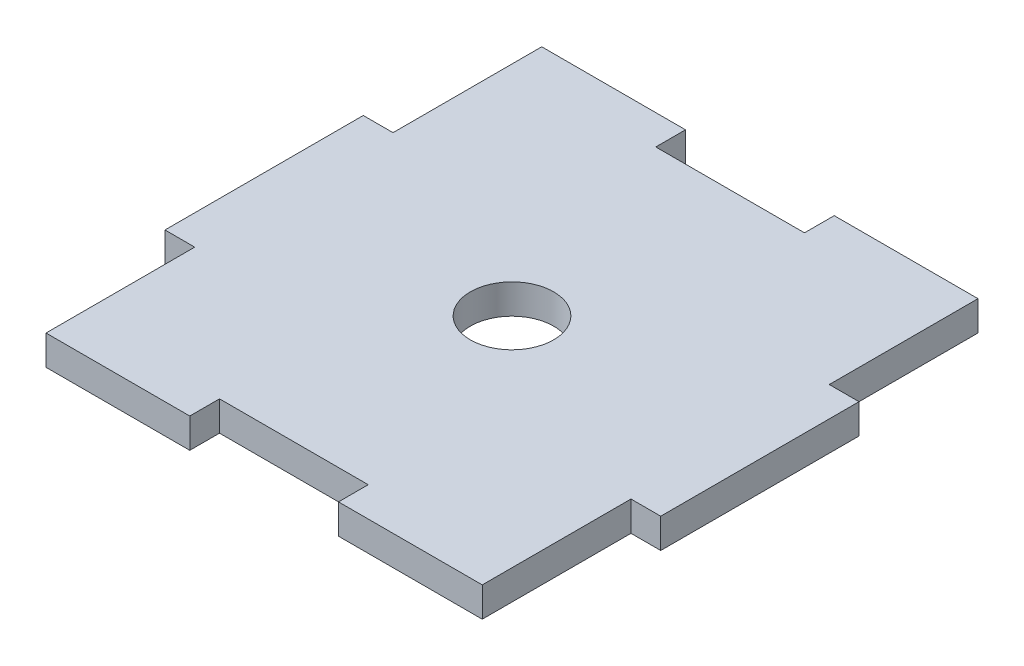
SolidWorks part; units mm, degrees
ref_plane "前视基准面" through (0, 0, 0) normal (0, 0, 1) x (1, 0, 0)
ref_plane "上视基准面" through (0, 0, 0) normal (0, 1, 0) x (1, 0, 0)
ref_plane "右视基准面" through (0, 0, 0) normal (1, 0, 0) x (0, 0, -1)
sketch "草图1" plane through (0, 0, 0) normal (0, 1, 0) x (1, 0, 0)
  line L0 (22, 25) -> (22, -25) construction
  line L1 (-25, 25) -> (25, 25) construction
  line L2 (-25, 25) -> (-25, -25) construction
  line L3 (-25, -25) -> (25, -25) construction
  line L4 (25, 25) -> (25, -25) construction
  line L5 (0, -25) -> (0, 25) construction
  line L6 (-25, 0) -> (25, 0) construction
  line L7 (-25, 22) -> (25, 22) construction
  line L8 (22, 25) -> (22, 10)
  line L9 (22, 10) -> (25, 10)
  line L10 (25, 10) -> (25, -10)
  line L11 (22, 25) -> (7.5, 25)
  line L12 (7.5, 25) -> (7.5, 22)
  line L13 (7.5, 22) -> (-7.5, 22)
  line L14 (-25, 10) -> (-25, -10)
  line L15 (-22, 10) -> (-25, 10)
  line L16 (-22, 25) -> (-22, 10)
  line L17 (-22, 25) -> (-7.5, 25)
  line L18 (-7.5, 25) -> (-7.5, 22)
  line L19 (22, -10) -> (25, -10)
  line L20 (22, -25) -> (22, -10)
  line L21 (22, -25) -> (7.5, -25)
  line L22 (7.5, -25) -> (7.5, -22)
  line L23 (7.5, -22) -> (-7.5, -22)
  line L24 (-7.5, -25) -> (-7.5, -22)
  line L25 (-22, -25) -> (-7.5, -25)
  line L26 (-22, -25) -> (-22, -10)
  line L27 (-22, -10) -> (-25, -10)
  circle A0 centre (0, 0) radius 4.2
  circle A1 centre (0, 0) radius 20 construction
  point P0 (0, 0)
  point P21 (0, 22)
  dimension "D1" = 8.4
  dimension "D2" = 40
  dimension "D3" = 50
  dimension "D4" = 50
  dimension "D5" = 3
  dimension "D6" = 3
  dimension "D7" = 20
  dimension "D8" = 15
extrude "凸台-拉伸1" add sketch "草图1" along normal blind 3
